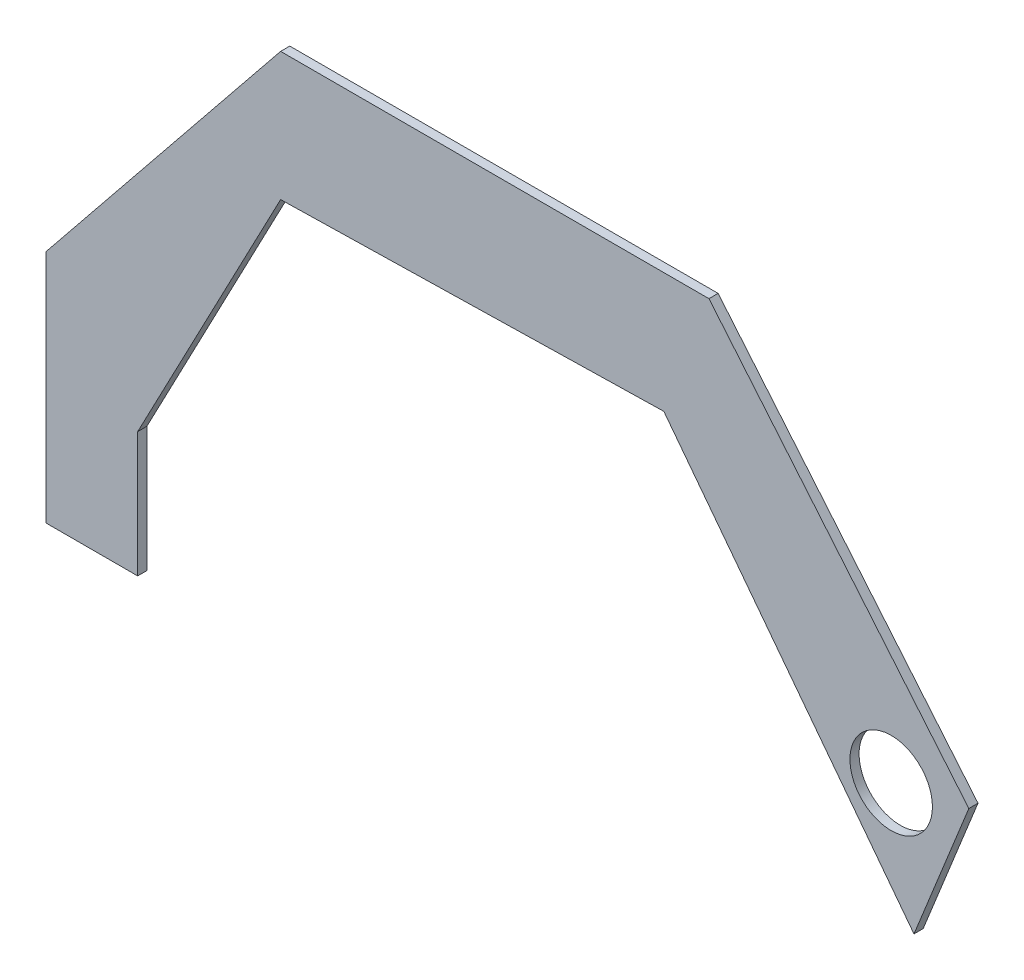
SolidWorks part; units mm, degrees
ref_plane "Front Plane" through (0, 0, 0) normal (0, 0, 1) x (1, 0, 0)
ref_plane "Top Plane" through (0, 0, 0) normal (0, 1, 0) x (1, 0, 0)
ref_plane "Right Plane" through (0, 0, 0) normal (1, 0, 0) x (0, 0, -1)
sketch "Sketch1" plane through (0, 0, 0) normal (0, 0, 1) x (1, 0, 0)
  line L2 (-154.0094, 151.208) -> (-235.2609, 50.5105)
  line L3 (-235.2609, 50.5105) -> (-235.2609, -30.8755)
  line L4 (-235.2609, -30.8755) -> (-203.5109, -30.8755)
  line L5 (-203.5109, -30.8755) -> (-203.5109, 12.4105)
  line L6 (-203.5109, 12.4105) -> (-154.0094, 106.758)
  line L8 (-154.0094, 151.208) -> (-154.0094, 106.758)
  line L9 (-235.2609, 50.5105) -> (-203.5109, 12.4105)
  line L10 (65.3339, -3.8218) -> (-21.2833, 109.591)
  line L11 (-21.2833, 109.591) -> (-154.0094, 106.758)
  line L12 (84.3271, 43.294) -> (-5.6685, 151.208)
  line L13 (-5.6685, 151.208) -> (-154.0094, 151.208)
  line L14 (-5.6685, 151.208) -> (-21.2833, 109.591)
  line L15 (84.3271, 43.294) -> (65.3339, -3.8218)
  point P2 (-203.5109, 12.4105)
  point P11 (-144.5313, 75.1371)
  point P12 (13.3556, 129.8876)
  point P13 (-151.7868, 136.1196)
  dimension "D1" = 31.75
  dimension "D2" = 50.8
  dimension "D3" = 44.45
  dimension "D4" = 38.1
  dimension "D5" = 44.45
extrude "Boss-Extrude2" add sketch "Sketch1" along normal blind 3.175
sketch "Sketch2" plane through (0, 0, 3.175) normal (0, 0, 1) x (1, 0, 0)
  circle A0 centre (57.4325, 37.4971) radius 14.2875
  point P2 (15.3416, 0)
  point P3 (52.1525, 0)
  point P4 (27.8286, 0)
  point P5 (0, 0)
  point P6 (28.3462, 5.0757)
  point P7 (32.9893, 30.7218)
  point P8 (57.4325, 37.4971)
  dimension "D1" = 28.575
extrude "Cut-Extrude1" cut sketch "Sketch2" against normal blind 3.175
